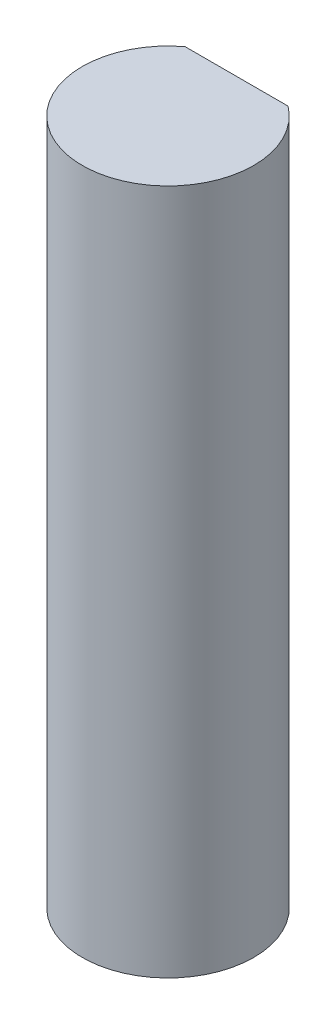
SolidWorks part; units mm, degrees
ref_plane "Front Plane" through (0, 0, 0) normal (0, 0, 1) x (1, 0, 0)
ref_plane "Top Plane" through (0, 0, 0) normal (0, 1, 0) x (1, 0, 0)
ref_plane "Right Plane" through (0, 0, 0) normal (1, 0, 0) x (0, 0, -1)
sketch "Sketch1" plane through (0, 0, 0) normal (0, 1, 0) x (1, 0, 0)
  line L0 (-1.905, 2.54) -> (1.905, 2.54)
  arc A0 (-1.905, 2.54) -> (1.905, 2.54) centre (0, 0) ccw
  dimension "D1" = 6.35
  dimension "D2" = 2.54
extrude "Boss-Extrude1" add sketch "Sketch1" along normal blind 25.4
